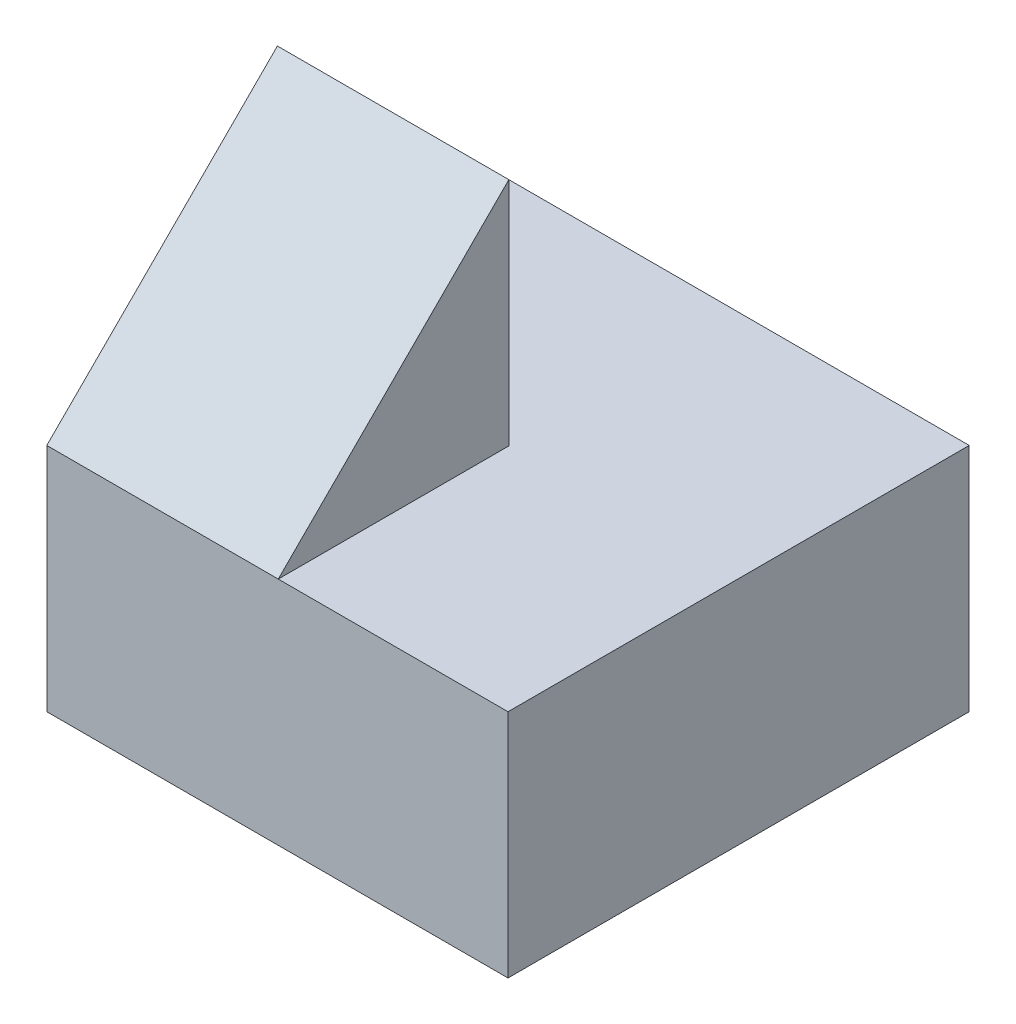
SolidWorks part; units mm, degrees
ref_plane "Front" through (0, 0, 0) normal (0, 0, 1) x (1, 0, 0)
ref_plane "Top" through (0, 0, 0) normal (0, 1, 0) x (1, 0, 0)
ref_plane "Right" through (0, 0, 0) normal (1, 0, 0) x (0, 0, -1)
sketch "Sketch1" plane through (0, 0, 0) normal (0, 1, 0) x (1, 0, 0)
  line L1 (0, 0) -> (4, 0)
  line L2 (0, 0) -> (0, 4)
  line L3 (0, 4) -> (4, 4)
  line L4 (4, 0) -> (4, 4)
  dimension "D1" = 4
  dimension "D2" = 4
extrude "Boss-Extrude1" add sketch "Sketch1" along normal blind 4
sketch "Sketch2" plane through (0, 4, 0) normal (0, 1, 0) x (1, 0, 0)
  line L0 (0, 0) -> (4, 0) construction
  line L5 (0, 2) -> (2.0075, 2)
  line L6 (0, 2) -> (0, 0)
  line L7 (0, 0) -> (2.0075, 0)
  line L8 (2.0075, 2) -> (2.0075, 0)
  line L9 (0, 4) -> (0, 0) construction
  line M1 (0, 4) -> (0, 0)
  line M2 (0, 0) -> (4, 0)
  line M3 (4, 0) -> (4, 4)
  line M4 (4, 4) -> (0, 4)
  dimension "D1" = 0
  dimension "D2" = 0
extrude "Cut-Extrude1" cut sketch "Sketch2" against normal blind 2 contours L8 L7 M4 M1 M2 M3
sketch "Sketch3" plane through (0, 0, 0) normal (-1, 0, 0) x (0, 0, 1)
  line L0 (-2, 4) -> (0, 2)
  line L1 (0, 4) -> (0, 0) construction
  line L2 (0, 2) -> (0, 4)
  line L3 (0, 4) -> (-2.1387, 4)
  line M1 (0, 4) -> (-2, 4)
  line M6 (0, 0) -> (0, 4)
extrude "Cut-Extrude2" cut sketch "Sketch3" against normal blind 10 contours L0 M1 M6
